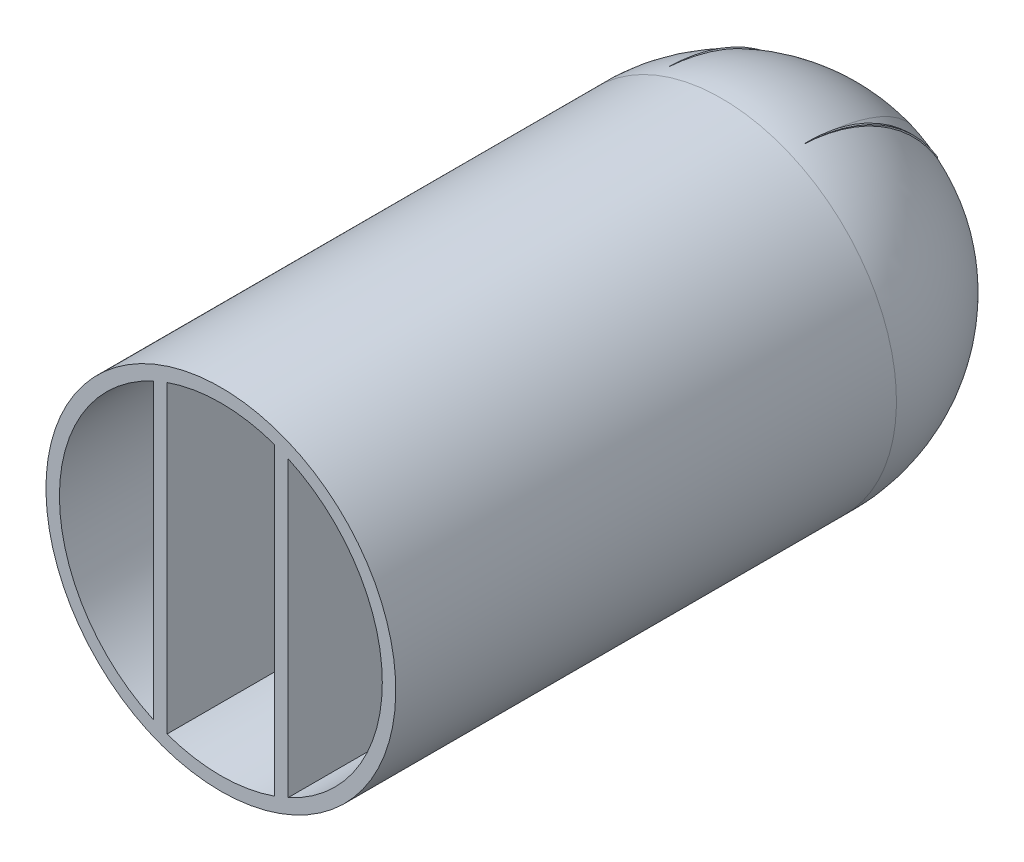
SolidWorks part; units mm, degrees
ref_plane "Front Plane" through (0, 0, 0) normal (0, 0, 1) x (1, 0, 0)
ref_plane "Top Plane" through (0, 0, 0) normal (0, 1, 0) x (1, 0, 0)
ref_plane "Right Plane" through (0, 0, 0) normal (1, 0, 0) x (0, 0, -1)
sketch "Sketch1" plane through (0, 0, 0) normal (1, 0, 0) x (0, 0, -1)
  line L0 (-50, 0) -> (50, 0) construction
  line L1 (-50, -24) -> (50, -24) construction
  line L2 (-50, -24) -> (-50, 24)
  line L3 (-50, 24) -> (50, 24) construction
  line L4 (50, -24) -> (50, 24) construction
  line L5 (-50, -24) -> (50, 24) construction
  line L6 (-50, 24) -> (50, -24) construction
  line L7 (0, 24) -> (0, -24) construction
  line L8 (26, 24) -> (-50, 24)
  line L9 (-7.8, -10.5) -> (33.2, -10.5)
  line L10 (-7.8, -10.5) -> (-7.8, 10.5)
  line L11 (-7.8, 10.5) -> (33.2, 10.5)
  line L12 (33.2, -10.5) -> (33.2, 10.5)
  line L13 (-7.8, -10.5) -> (33.2, 10.5) construction
  line L14 (-7.8, 10.5) -> (33.2, -10.5) construction
  line L15 (-11.3, -5) -> (36.7, -5) construction
  line L16 (-11.3, -5) -> (-11.3, 5) construction
  line L17 (-11.3, 5) -> (36.7, 5) construction
  line L18 (36.7, -5) -> (36.7, 5) construction
  line L19 (-11.3, -5) -> (36.7, 5) construction
  line L20 (-11.3, 5) -> (36.7, -5) construction
  line L21 (26, -24) -> (-50, -24)
  circle A0 centre (36.7, 5) radius 2.5
  circle A1 centre (36.7, -5) radius 2.5
  circle A2 centre (-11.3, -5) radius 2.5
  circle A3 centre (-11.3, 5) radius 2.5
  arc A4 (26, 24) -> (26, -24) centre (26, 0) cw
  point P0 (0, 0)
  point P10 (12.7, 0)
  point P16 (12.7, 0)
  point P27 (0, 0)
  dimension "D6" = 5
  dimension "D1" = 48
  dimension "D2" = 100
  dimension "D3" = 41
  dimension "D4" = 21
  dimension "D5" = 7.2
  dimension "D7" = 48
  dimension "D8" = 10
extrude "Boss-Extrude1" add sketch "Sketch1" along normal blind 2
ref_plane "Plane1" through (-8, 0, 0) normal (-1, 0, 0) x (0, 0, 1)
ref_plane "Plane2" through (-16, 0, 0) normal (-1, 0, 0) x (0, 0, 1)
sketch "Sketch4" plane through (-8, 0, 0) normal (-1, 0, 0) x (0, 0, 1)
  line L0 (-50, 0) -> (50, 0) construction
  line L1 (50, 24) -> (50, -24) construction
  line L2 (50, 26) -> (-24.4317, 26)
  line L3 (50, 26) -> (50, 24)
  line L4 (50, 24) -> (-26.0643, 24)
  line L6 (-50.3, 0) -> (-52.3, 0)
  arc A0 (-26, 24) -> (-26, -24) centre (-26, 0) ccw construction
  arc A2 (-26.0643, 24) -> (-50.3, 0) centre (-26.0643, -0.2368) ccw
  arc A3 (-24.4317, 26) -> (-52.3, 0) centre (-25.3913, -0.9068) ccw
  dimension "D1" = 26
  dimension "D2" = 2
  dimension "D3" = 2
  dimension "D4" = 52.3
revolve "Revolve1" add sketch "Sketch4" angle 360 about L0
sketch "Sketch6" plane through (-16, 0, 0) normal (-1, 0, 0) x (0, 0, 1)
  line L0 (-26, 24) -> (50, 24)
  line L1 (50, 24) -> (50, -24)
  line L2 (50, -24) -> (-26, -24)
  line L3 (-33.2, -10.5) -> (-33.2, 10.5) construction
  line L4 (-33.2, -10.5) -> (7.8, -10.5)
  line L5 (-33.2, -10.5) -> (-33.2, 10.5)
  line L6 (-33.2, 10.5) -> (7.8, 10.5)
  line L7 (7.8, -10.5) -> (7.8, 10.5)
  line L8 (-33.2, -10.5) -> (7.8, 10.5) construction
  line L9 (-33.2, 10.5) -> (7.8, -10.5) construction
  line L10 (7.8, -10.5) -> (-33.2, -10.5) construction
  arc A0 (-26, 24) -> (-26, -24) centre (-26, 0) ccw
  point P9 (-12.7, 0)
  point P19 (0, 0)
  point P20 (0, 0)
  point P21 (0, 0)
  dimension "D1" = 62.7
  dimension "D2" = 13.3
  dimension "D3" = 48
  dimension "D4" = 76
extrude "Boss-Extrude4" add sketch "Sketch6" along normal blind 2
sketch "Sketch7" plane through (-8, 0, 0) normal (-1, 0, 0) x (0, 0, 1)
  line L0 (0, 0) -> (-52.5, 0) construction
  line L1 (-58.5, -26.3327) -> (-46.5, -26.3327)
  line L2 (-58.5, -26.3327) -> (-58.5, 26.3327)
  line L3 (-58.5, 26.3327) -> (-46.5, 26.3327)
  line L4 (-46.5, -26.3327) -> (-46.5, 26.3327)
  line L5 (-58.5, -26.3327) -> (-46.5, 26.3327) construction
  line L6 (-58.5, 26.3327) -> (-46.5, -26.3327) construction
  point P0 (-52.5, 0)
  dimension "D1" = 52.5
  dimension "D2" = 12
extrude "Cut-Extrude1" cut sketch "Sketch7" against normal through all both and the other way through all
